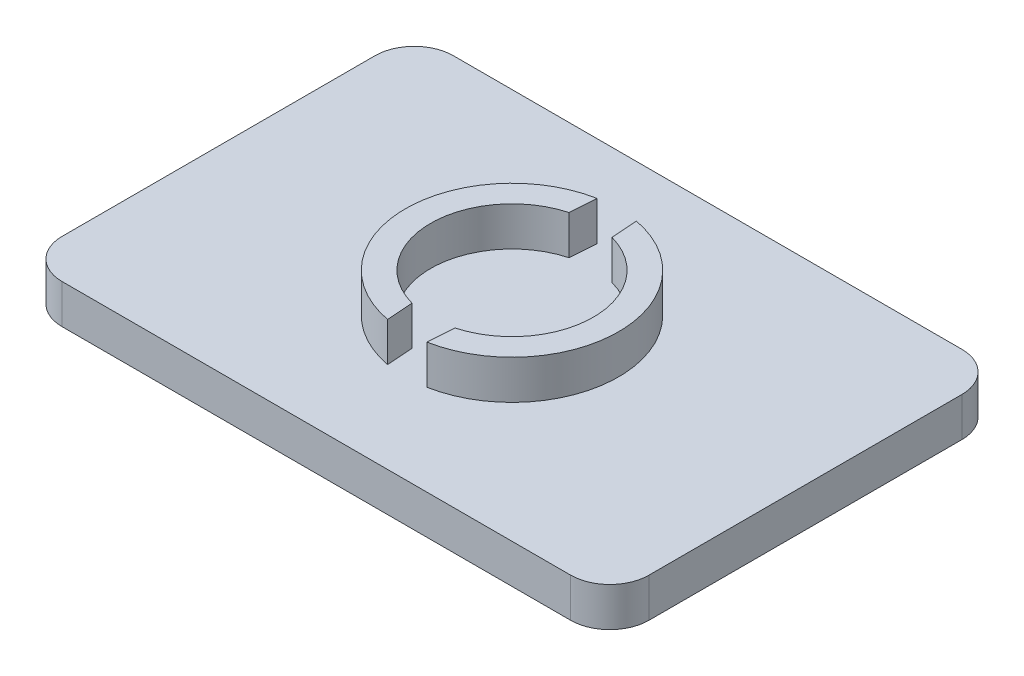
SolidWorks part; units mm, degrees
ref_plane "Front Plane" through (0, 0, 0) normal (0, 0, 1) x (1, 0, 0)
ref_plane "Top Plane" through (0, 0, 0) normal (0, 1, 0) x (1, 0, 0)
ref_plane "Right Plane" through (0, 0, 0) normal (1, 0, 0) x (0, 0, -1)
sketch "Sketch1" plane through (0, 0, 0) normal (0, 1, 0) x (1, 0, 0)
  line L1 (38.1, -25.4) -> (-38.1, -25.4)
  line L2 (38.1, -25.4) -> (38.1, 25.4)
  line L3 (38.1, 25.4) -> (-38.1, 25.4)
  line L4 (-38.1, -25.4) -> (-38.1, 25.4)
  line L5 (38.1, -25.4) -> (-38.1, 25.4) construction
  line L6 (38.1, 25.4) -> (-38.1, -25.4) construction
  circle A0 centre (0, 0) radius 5.0577
  point P0 (0, 0)
  point P5 (0, 0)
  point P8 (0, 0)
  dimension "D1" = 76.2
  dimension "D2" = 50.8
extrude "Boss-Extrude1" add sketch "Sketch1" along normal blind 5.08 contours L2 L1 L4 L3
fillet "Fillet1" radius 5.08 4 edges at (-38.1, 2.54, -25.4) (38.1, 2.54, -25.4) (38.1, 2.54, 25.4) (-38.1, 2.54, 25.4)
sketch "Sketch2" plane through (0, 5.08, 0) normal (0, 1, 0) x (1, 0, 0)
  line L0 (0, 0) -> (-2.54, 13.6057) construction
  line L1 (-2.54, 13.6057) -> (2.54, 13.6057) construction
  line L2 (-2.54, -13.6057) -> (2.54, -13.6057) construction
  line L3 (-2.794, 10.191) -> (2.794, 10.191) construction
  line L4 (0, 0) -> (2.54, 13.6057) construction
  line L5 (-38.1, 0) -> (38.1, 0) construction
  line L6 (-38.1, 20.32) -> (-38.1, -20.32) construction
  line L7 (38.1, -20.32) -> (38.1, 20.32) construction
  line L8 (0, 0) -> (2.54, -13.6057) construction
  line L9 (0, 0) -> (-2.54, -13.6057) construction
  line L10 (-2.794, -10.191) -> (2.794, -10.191) construction
  line L11 (0, 0) -> (10.16, 2.9045) construction
  line L12 (0, 0) -> (-9.2595, 5.0915) construction
  line L13 (0, 0) -> (12.9981, 12.9981) construction
  line L14 (0, 0) -> (-16.836, 7.3791) construction
  line L15 (0, 25.4) -> (0, -25.4) construction
  line L16 (33.02, 25.4) -> (-33.02, 25.4) construction
  line L17 (33.02, -25.4) -> (-33.02, -25.4) construction
  line L18 (2.794, 10.191) -> (2.54, 13.6057)
  line L19 (-2.794, 10.191) -> (-2.54, 13.6057)
  line L20 (-2.54, -13.6057) -> (-2.794, -10.191)
  line L21 (2.54, -13.6057) -> (2.794, -10.191)
  arc A0 (-2.54, 13.6057) -> (-2.54, -13.6057) centre (0, 0) ccw
  arc A1 (-2.794, 10.191) -> (-2.794, -10.191) centre (0, 0) ccw
  arc A2 (2.54, -13.6057) -> (2.54, 13.6057) centre (0, 0) ccw
  arc A3 (2.794, -10.191) -> (2.794, 10.191) centre (0, 0) ccw
  circle A4 centre (0, 0) radius 18.3821
  point P27 (0, 13.6057)
  point P28 (0, 10.191)
  dimension "D1" = 5.588
  dimension "D2" = 5.08
  dimension "D3" = 10.16
extrude "Boss-Extrude2" add sketch "Sketch2" along normal blind 5.08 from surface at 0 contours A1 L20 A0 L19 | A2 L18 A3 L21 starting at face at (0, 5.08, 0)
sketch "Sketch4" plane through (0, 5.08, 0) normal (0, 1, 0) x (1, 0, 0)
  circle A0 centre (0, 0) radius 4.5251
